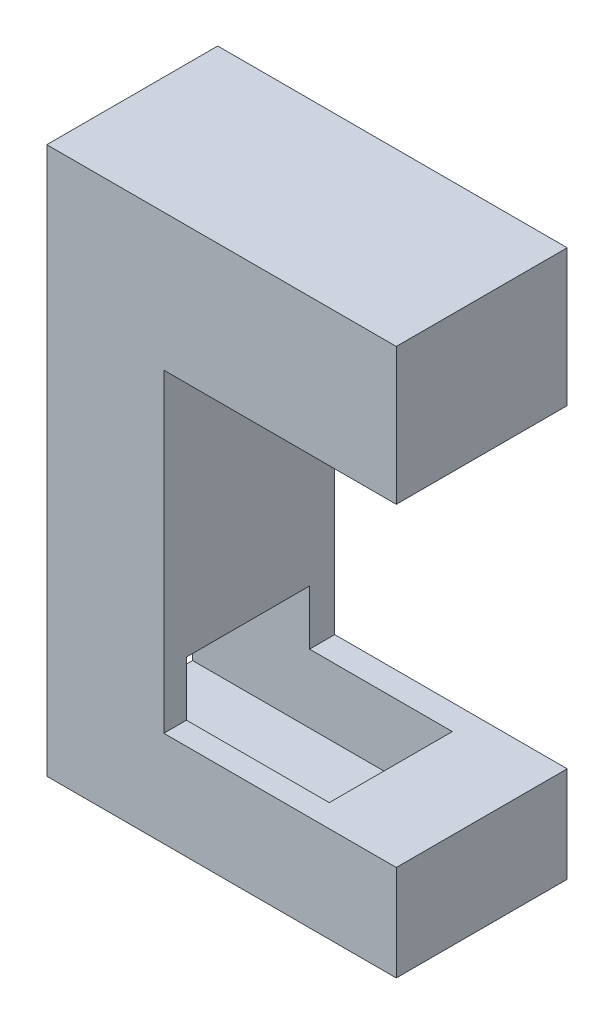
SolidWorks part; units mm, degrees
ref_plane "Front Plane" through (0, 0, 0) normal (0, 0, 1) x (1, 0, 0)
ref_plane "Top Plane" through (0, 0, 0) normal (0, 1, 0) x (1, 0, 0)
ref_plane "Right Plane" through (0, 0, 0) normal (1, 0, 0) x (0, 0, -1)
sketch "Sketch3" plane through (0, 0, 0) normal (0, 0, 1) x (1, 0, 0)
  line L0 (51.4444, 20.4428) -> (25.8862, 20.4428)
  line L1 (25.8862, 20.4428) -> (25.8862, -19.5572)
  line L2 (25.8862, -19.5572) -> (51.4444, -19.5572)
  line L3 (51.4444, -19.5572) -> (51.4444, -12.5572)
  line L4 (51.4444, -12.5572) -> (34.4444, -12.5572)
  line L5 (34.4444, -12.5572) -> (34.4444, 10.4428)
  line L6 (34.4444, 10.4428) -> (51.4444, 10.4428)
  line L7 (51.4444, 20.4428) -> (51.4444, 10.4428)
extrude "Boss-Extrude1" add sketch "Sketch3" along normal blind 12.5
sketch "Sketch4" plane through (0, 10.4428, 0) normal (0, -1, 0) x (1, 0, 0)
  line L0 (25.8862, 12.5) -> (25.8862, 0) construction
  line L1 (37.8862, 9.25) -> (41.8862, 9.25)
  line L2 (37.8862, 9.25) -> (37.8862, 3.25)
  line L3 (37.8862, 3.25) -> (41.8862, 3.25)
  line L4 (41.8862, 9.25) -> (41.8862, 3.25)
  line L5 (37.8862, 9.25) -> (41.8862, 3.25) construction
  line L6 (37.8862, 3.25) -> (41.8862, 9.25) construction
  line L8 (51.4444, 0) -> (25.8862, 0) construction
  point P0 (39.8862, 6.25)
  dimension "D1" = 12
  dimension "D2" = 6.25
sketch "Sketch6" plane through (25.8862, 0, 0) normal (-1, 0, 0) x (0, 0, 1)
  line L0 (12.5, -19.5572) -> (0, -19.5572) construction
  line L1 (1.8426, -8.5572) -> (10.8426, -8.5572)
  line L2 (1.8426, -8.5572) -> (1.8426, -17.5572)
  line L3 (1.8426, -17.5572) -> (10.8426, -17.5572)
  line L4 (10.8426, -8.5572) -> (10.8426, -17.5572)
  line L5 (1.8426, -8.5572) -> (10.8426, -17.5572) construction
  line L6 (1.8426, -17.5572) -> (10.8426, -8.5572) construction
  point P0 (6.3426, -13.0572)
  point P5 (6.25, 15.2128)
  point P6 (6.25, -14.5743)
  point P7 (6.1277, -13.859)
  point P8 (6.5576, -13.9307)
  point P9 (6.1993, -14.074)
  point P10 (0, 0)
  point P11 (0, 0)
  point P12 (0, 0)
  point P13 (6.3426, -14.074)
  point P14 (0, 0)
  point P15 (0, 0)
  dimension "D1" = 2
extrude "Cut-Extrude2" cut sketch "Sketch6" against normal blind 19
